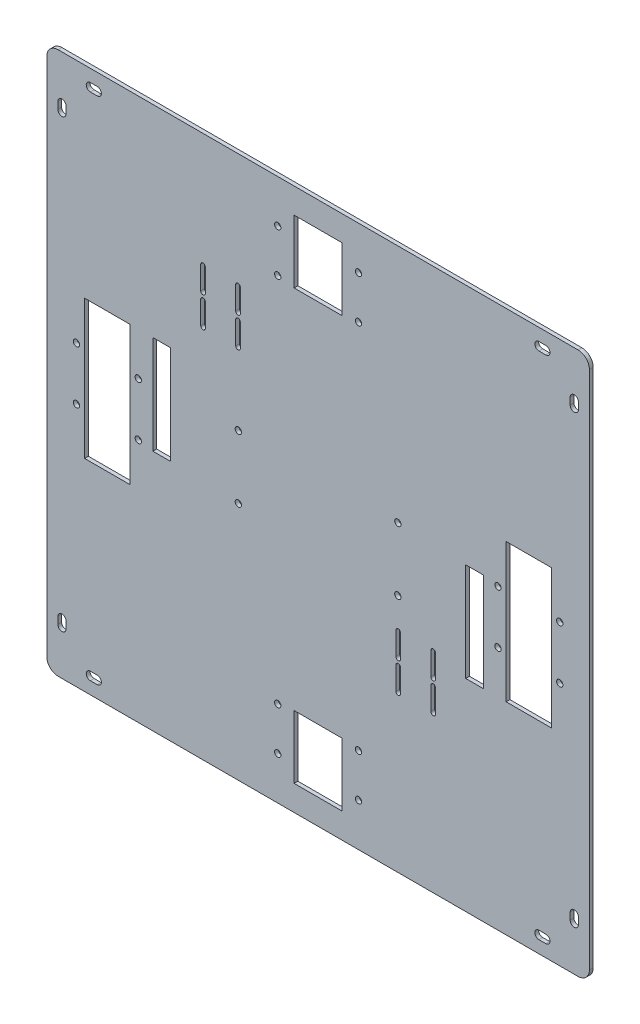
SolidWorks part; units mm, degrees
material "Alloy Steel (SS)"
ref_plane "Front Plane" through (0, 0, 0) normal (0, 0, 1) x (1, 0, 0)
ref_plane "Top Plane" through (0, 0, 0) normal (0, 1, 0) x (1, 0, 0)
ref_plane "Right Plane" through (0, 0, 0) normal (1, 0, 0) x (0, 0, -1)
sketch "Sketch1" plane through (0, 0, 0) normal (0, 0, 1) x (1, 0, 0)
  line L0 (0, 30.6518) -> (0, 116.7974) construction
  line L1 (215, 245.6518) -> (-215, 245.6518)
  line L2 (215, 245.6518) -> (215, -184.3482)
  line L3 (215, -184.3482) -> (-215, -184.3482)
  line L4 (-215, 245.6518) -> (-215, -184.3482)
  line L5 (215, 245.6518) -> (-215, -184.3482) construction
  line L6 (215, -184.3482) -> (-215, 245.6518) construction
  line L13 (0, 30.6518) -> (-105.2674, 30.6518) construction
  point P0 (0, 30.6518)
  dimension "D1" = 430
  dimension "D2" = 430
extrude "Boss-Extrude1" add sketch "Sketch1" along normal blind 3
sketch "Sketch6" plane through (0, 0, 3) normal (0, 0, 1) x (1, 0, 0)
  line L0 (-199.75, 204.6518) -> (-199.75, 210.1518) construction
  line L1 (-206.25, 210.1518) -> (-206.25, 204.6518) construction
  line L2 (-199.75, 204.6518) -> (-199.75, 210.1518)
  line L3 (-206.25, 210.1518) -> (-206.25, 204.6518)
  line L20 (-180.5, 229.4018) -> (-175, 229.4018) construction
  line L21 (-175, 235.9018) -> (-180.5, 235.9018) construction
  line L22 (-180.5, 229.4018) -> (-175, 229.4018)
  line L23 (-175, 235.9018) -> (-180.5, 235.9018)
  line L40 (0, 30.6518) -> (-215, 30.6518) construction
  line L41 (0, 30.6518) -> (-215, 30.6518) construction
  line L50 (-175, -174.5982) -> (-180.5, -174.5982)
  line L51 (-180.5, -168.0982) -> (-175, -168.0982)
  line L60 (-206.25, -148.8482) -> (-206.25, -143.3482)
  line L61 (-199.75, -143.3482) -> (-199.75, -148.8482)
  line L62 (0, 30.6518) -> (0, 245.6518) construction
  line L63 (0, 30.6518) -> (0, 245.6518) construction
  line L64 (199.75, -143.3482) -> (199.75, -148.8482)
  line L65 (206.25, -148.8482) -> (206.25, -143.3482)
  line L74 (180.5, -168.0982) -> (175, -168.0982)
  line L75 (175, -174.5982) -> (180.5, -174.5982)
  line L92 (175, 235.9018) -> (180.5, 235.9018)
  line L93 (180.5, 229.4018) -> (175, 229.4018)
  line L102 (206.25, 210.1518) -> (206.25, 204.6518)
  line L103 (199.75, 204.6518) -> (199.75, 210.1518)
  arc A0 (-206.25, 204.6518) -> (-199.75, 204.6518) centre (-203, 204.6518) ccw construction
  arc A1 (-199.75, 210.1518) -> (-206.25, 210.1518) centre (-203, 210.1518) ccw construction
  arc A2 (-206.25, 204.6518) -> (-199.75, 204.6518) centre (-203, 204.6518) ccw
  arc A3 (-199.75, 210.1518) -> (-206.25, 210.1518) centre (-203, 210.1518) ccw
  arc A4 (-175, 229.4018) -> (-175, 235.9018) centre (-175, 232.6518) ccw construction
  arc A5 (-180.5, 235.9018) -> (-180.5, 229.4018) centre (-180.5, 232.6518) ccw construction
  arc A6 (-175, 229.4018) -> (-175, 235.9018) centre (-175, 232.6518) ccw
  arc A7 (-180.5, 235.9018) -> (-180.5, 229.4018) centre (-180.5, 232.6518) ccw
  arc A8 (-180.5, -174.5982) -> (-180.5, -168.0982) centre (-180.5, -171.3482) cw
  arc A9 (-175, -168.0982) -> (-175, -174.5982) centre (-175, -171.3482) cw
  arc A10 (-199.75, -148.8482) -> (-206.25, -148.8482) centre (-203, -148.8482) cw
  arc A11 (-206.25, -143.3482) -> (-199.75, -143.3482) centre (-203, -143.3482) cw
  arc A12 (206.25, -143.3482) -> (199.75, -143.3482) centre (203, -143.3482) ccw
  arc A13 (199.75, -148.8482) -> (206.25, -148.8482) centre (203, -148.8482) ccw
  arc A14 (175, -168.0982) -> (175, -174.5982) centre (175, -171.3482) ccw
  arc A15 (180.5, -174.5982) -> (180.5, -168.0982) centre (180.5, -171.3482) ccw
  arc A16 (180.5, 235.9018) -> (180.5, 229.4018) centre (180.5, 232.6518) cw
  arc A17 (175, 229.4018) -> (175, 235.9018) centre (175, 232.6518) cw
  arc A18 (199.75, 210.1518) -> (206.25, 210.1518) centre (203, 210.1518) cw
  arc A19 (206.25, 204.6518) -> (199.75, 204.6518) centre (203, 204.6518) cw
extrude "Cut-Extrude5" cut sketch "Sketch6" against normal up to next
sketch "Sketch7" plane through (0, 0, 0) normal (0, 0, -1) x (-1, 0, 0)
  line L0 (0, 30.6518) -> (0, -184.3482) construction
  line L1 (185, -24.3482) -> (149, -24.3482)
  line L2 (185, -24.3482) -> (185, 85.6518)
  line L3 (185, 85.6518) -> (149, 85.6518)
  line L4 (149, -24.3482) -> (149, 85.6518)
  line L5 (185, -24.3482) -> (149, 85.6518) construction
  line L6 (185, 85.6518) -> (149, -24.3482) construction
  line L7 (215, -184.3482) -> (-215, -184.3482) construction
  line L8 (-185, 85.6518) -> (-149, -24.3482) construction
  line L9 (-185, -24.3482) -> (-149, 85.6518) construction
  line L10 (-149, -24.3482) -> (-149, 85.6518)
  line L11 (-185, 85.6518) -> (-149, 85.6518)
  line L12 (-185, -24.3482) -> (-185, 85.6518)
  line L13 (-185, -24.3482) -> (-149, -24.3482)
  line L14 (215, 245.6518) -> (215, -184.3482) construction
  point P0 (167, 30.6518)
  point P15 (-167, 30.6518)
  dimension "D1" = 36
  dimension "D2" = 110
  dimension "D3" = 30
extrude "Cut-Extrude6" cut sketch "Sketch7" against normal through all
sketch "Sketch9" plane through (0, 0, 0) normal (0, 0, -1) x (-1, 0, 0)
  line L0 (215, -184.3482) -> (-215, -184.3482) construction
  line L1 (-19, -164.3482) -> (19, -164.3482)
  line L2 (-19, -164.3482) -> (-19, -114.3482)
  line L3 (-19, -114.3482) -> (19, -114.3482)
  line L4 (19, -164.3482) -> (19, -114.3482)
  line L5 (0, 30.6518) -> (215, 30.6518) construction
  line L6 (0, 30.6518) -> (0, -148.8482) construction
  line L7 (19, 225.6518) -> (19, 175.6518)
  line L8 (-19, 175.6518) -> (19, 175.6518)
  line L9 (-19, 225.6518) -> (-19, 175.6518)
  line L10 (-19, 225.6518) -> (19, 225.6518)
  point P0 (0, -148.8482)
  point P17 (0, 210.1518)
  dimension "D1" = 20
  dimension "D2" = 38
  dimension "D3" = 50
extrude "Cut-Extrude7" cut sketch "Sketch9" against normal through all
sketch "Sketch10" plane through (0, 0, 0) normal (0, 0, -1) x (-1, 0, 0)
  line L0 (0, 30.6518) -> (215, 30.6518) construction
  circle A0 centre (32, -150.3482) radius 2.5 construction
  circle A1 centre (32, -150.3482) radius 2.5
  circle A2 centre (32, -116.3482) radius 2.5 construction
  circle A3 centre (32, -116.3482) radius 2.5
  circle A4 centre (-32, -116.3482) radius 2.5 construction
  circle A5 centre (-32, -116.3482) radius 2.5
  circle A6 centre (-32, -150.3482) radius 2.5 construction
  circle A7 centre (-32, -150.3482) radius 2.5
  circle A8 centre (-32, 211.6518) radius 2.5
  circle A9 centre (-32, 177.6518) radius 2.5
  circle A10 centre (32, 177.6518) radius 2.5
  circle A11 centre (32, 211.6518) radius 2.5
extrude "Cut-Extrude8" cut sketch "Sketch10" against normal through all
sketch "Sketch14" plane through (0, 0, 0) normal (0, 0, -1) x (-1, 0, 0)
  line L28 (215, 245.6518) -> (215, -184.3482) construction
  line L33 (117, 85.6518) -> (117, 7.6518)
  line L34 (131, 85.6518) -> (117, 85.6518)
  line L35 (131, 7.6518) -> (131, 85.6518)
  line L36 (-215, -184.3482) -> (-215, 245.6518) construction
  line L40 (-131, -24.3482) -> (-117, -24.3482)
  line L41 (-131, 53.6518) -> (-131, -24.3482)
  line L42 (-117, 53.6518) -> (-131, 53.6518)
  line L43 (-117, -24.3482) -> (-117, 53.6518)
  line L44 (131, 7.6518) -> (117, 7.6518)
  line L45 (185, 85.6518) -> (149, 85.6518) construction
  line L49 (-185, -24.3482) -> (-149, -24.3482) construction
  dimension "D2" = 84
  dimension "D3" = 14
  dimension "D1" = 84
  dimension "D4" = 14
  dimension "D5" = 78
  dimension "D6" = 78
extrude "Cut-Extrude11" cut sketch "Sketch14" against normal through all
sketch "Sketch15" plane through (0, 0, 0) normal (0, 0, -1) x (-1, 0, 0)
  line L0 (0, -184.3482) -> (0, 245.6518) construction
  line L18 (-61.63, -53.8932) -> (-61.63, -48.6932)
  line L19 (-65.28, -48.6932) -> (-65.28, -53.8932)
  line L20 (-61.63, -53.8932) -> (-61.63, -48.6932)
  line L21 (-65.28, -48.6932) -> (-65.28, -53.8932)
  line L22 (-61.63, -30.0032) -> (-61.63, -24.8032)
  line L23 (-65.28, -24.8032) -> (-65.28, -30.0032)
  line L24 (-61.63, -30.0032) -> (-61.63, -24.8032)
  line L25 (-65.28, -24.8032) -> (-65.28, -30.0032)
  line L26 (-89.38, -53.8932) -> (-89.38, -48.6932)
  line L27 (-93.03, -48.6932) -> (-93.03, -53.8932)
  line L28 (-89.38, -53.8932) -> (-89.38, -48.6932)
  line L29 (-93.03, -48.6932) -> (-93.03, -53.8932)
  line L30 (-89.38, -30.0032) -> (-89.38, -24.8032)
  line L31 (-93.03, -24.8032) -> (-93.03, -30.0032)
  line L32 (-89.38, -30.0032) -> (-89.38, -24.8032)
  line L33 (-93.03, -24.8032) -> (-93.03, -30.0032)
  line L50 (-63.455, -53.8932) -> (-63.455, -60.8932) construction
  line L51 (-61.63, -53.8932) -> (-61.63, -60.8932)
  line L52 (-65.28, -53.8932) -> (-65.28, -60.8932)
  line L53 (-91.205, -53.8932) -> (-91.205, -60.8932) construction
  line L54 (-89.38, -53.8932) -> (-89.38, -60.8932)
  line L55 (-93.03, -53.8932) -> (-93.03, -60.8932)
  line L56 (-63.455, -30.0032) -> (-63.455, -37.0032) construction
  line L57 (-61.63, -30.0032) -> (-61.63, -37.0032)
  line L58 (-65.28, -30.0032) -> (-65.28, -37.0032)
  line L59 (-91.205, -30.0032) -> (-91.205, -37.0032) construction
  line L60 (-89.38, -30.0032) -> (-89.38, -37.0032)
  line L61 (-93.03, -30.0032) -> (-93.03, -37.0032)
  line L62 (-63.455, -24.8032) -> (-63.455, -18.8032) construction
  line L63 (-65.28, -24.8032) -> (-65.28, -18.8032)
  line L64 (-61.63, -24.8032) -> (-61.63, -18.8032)
  line L65 (-63.455, -48.6932) -> (-63.455, -42.6932) construction
  line L66 (-65.28, -48.6932) -> (-65.28, -42.6932)
  line L67 (-61.63, -48.6932) -> (-61.63, -42.6932)
  line L68 (-91.205, -48.6932) -> (-91.205, -42.6932) construction
  line L69 (-93.03, -48.6932) -> (-93.03, -42.6932)
  line L70 (-89.38, -48.6932) -> (-89.38, -42.6932)
  line L71 (-91.205, -24.8032) -> (-91.205, -18.8032) construction
  line L72 (-93.03, -24.8032) -> (-93.03, -18.8032)
  line L73 (-89.38, -24.8032) -> (-89.38, -18.8032)
  line L103 (1.25, 31.6518) -> (-215, 31.6518) construction
  line L104 (-215, -184.3482) -> (-215, 245.6518) construction
  line L178 (91.205, 118.7587) -> (91.205, 112.7587) construction
  line L179 (93.03, 118.7587) -> (93.03, 112.7587)
  line L180 (89.38, 118.7587) -> (89.38, 112.7587)
  line L181 (91.205, 142.6487) -> (91.205, 136.6487) construction
  line L182 (93.03, 142.6487) -> (93.03, 136.6487)
  line L183 (89.38, 142.6487) -> (89.38, 136.6487)
  line L184 (63.455, 142.6487) -> (63.455, 136.6487) construction
  line L185 (65.28, 142.6487) -> (65.28, 136.6487)
  line L186 (61.63, 142.6487) -> (61.63, 136.6487)
  line L187 (63.455, 118.7587) -> (63.455, 112.7587) construction
  line L188 (65.28, 118.7587) -> (65.28, 112.7587)
  line L189 (61.63, 118.7587) -> (61.63, 112.7587)
  line L190 (91.205, 123.9587) -> (91.205, 130.9587) construction
  line L191 (89.38, 123.9587) -> (89.38, 130.9587)
  line L192 (93.03, 123.9587) -> (93.03, 130.9587)
  line L193 (63.455, 123.9587) -> (63.455, 130.9587) construction
  line L194 (61.63, 123.9587) -> (61.63, 130.9587)
  line L195 (65.28, 123.9587) -> (65.28, 130.9587)
  line L196 (91.205, 147.8487) -> (91.205, 154.8487) construction
  line L197 (89.38, 147.8487) -> (89.38, 154.8487)
  line L198 (93.03, 147.8487) -> (93.03, 154.8487)
  line L199 (63.455, 147.8487) -> (63.455, 154.8487) construction
  line L200 (61.63, 147.8487) -> (61.63, 154.8487)
  line L201 (65.28, 147.8487) -> (65.28, 154.8487)
  line L202 (61.63, 147.8487) -> (61.63, 142.6487)
  line L203 (65.28, 142.6487) -> (65.28, 147.8487)
  line L204 (61.63, 123.9587) -> (61.63, 118.7587)
  line L205 (65.28, 118.7587) -> (65.28, 123.9587)
  line L206 (89.38, 147.8487) -> (89.38, 142.6487)
  line L207 (93.03, 142.6487) -> (93.03, 147.8487)
  line L208 (89.38, 123.9587) -> (89.38, 118.7587)
  line L209 (93.03, 118.7587) -> (93.03, 123.9587)
  arc A18 (-65.28, -53.8932) -> (-61.63, -53.8932) centre (-63.455, -53.8932) ccw
  arc A19 (-61.63, -48.6932) -> (-65.28, -48.6932) centre (-63.455, -48.6932) ccw
  arc A20 (-65.28, -53.8932) -> (-61.63, -53.8932) centre (-63.455, -53.8932) ccw
  arc A21 (-61.63, -48.6932) -> (-65.28, -48.6932) centre (-63.455, -48.6932) ccw
  arc A22 (-61.63, -24.8032) -> (-65.28, -24.8032) centre (-63.455, -24.8032) ccw
  arc A23 (-65.28, -30.0032) -> (-61.63, -30.0032) centre (-63.455, -30.0032) ccw
  arc A24 (-61.63, -24.8032) -> (-65.28, -24.8032) centre (-63.455, -24.8032) ccw
  arc A25 (-65.28, -30.0032) -> (-61.63, -30.0032) centre (-63.455, -30.0032) ccw
  arc A26 (-93.03, -53.8932) -> (-89.38, -53.8932) centre (-91.205, -53.8932) ccw
  arc A27 (-89.38, -48.6932) -> (-93.03, -48.6932) centre (-91.205, -48.6932) ccw
  arc A28 (-93.03, -53.8932) -> (-89.38, -53.8932) centre (-91.205, -53.8932) ccw
  arc A29 (-89.38, -48.6932) -> (-93.03, -48.6932) centre (-91.205, -48.6932) ccw
  arc A30 (-89.38, -24.8032) -> (-93.03, -24.8032) centre (-91.205, -24.8032) ccw
  arc A31 (-93.03, -30.0032) -> (-89.38, -30.0032) centre (-91.205, -30.0032) ccw
  arc A32 (-89.38, -24.8032) -> (-93.03, -24.8032) centre (-91.205, -24.8032) ccw
  arc A33 (-93.03, -30.0032) -> (-89.38, -30.0032) centre (-91.205, -30.0032) ccw
  arc A44 (-61.63, -53.8932) -> (-65.28, -53.8932) centre (-63.455, -53.8932) ccw
  arc A45 (-65.28, -60.8932) -> (-61.63, -60.8932) centre (-63.455, -60.8932) ccw
  arc A46 (-89.38, -53.8932) -> (-93.03, -53.8932) centre (-91.205, -53.8932) ccw
  arc A47 (-93.03, -60.8932) -> (-89.38, -60.8932) centre (-91.205, -60.8932) ccw
  arc A48 (-61.63, -30.0032) -> (-65.28, -30.0032) centre (-63.455, -30.0032) ccw
  arc A49 (-65.28, -37.0032) -> (-61.63, -37.0032) centre (-63.455, -37.0032) ccw
  arc A50 (-89.38, -30.0032) -> (-93.03, -30.0032) centre (-91.205, -30.0032) ccw
  arc A51 (-93.03, -37.0032) -> (-89.38, -37.0032) centre (-91.205, -37.0032) ccw
  arc A52 (-65.28, -24.8032) -> (-61.63, -24.8032) centre (-63.455, -24.8032) ccw
  arc A53 (-61.63, -18.8032) -> (-65.28, -18.8032) centre (-63.455, -18.8032) ccw
  arc A54 (-65.28, -48.6932) -> (-61.63, -48.6932) centre (-63.455, -48.6932) ccw
  arc A55 (-61.63, -42.6932) -> (-65.28, -42.6932) centre (-63.455, -42.6932) ccw
  arc A56 (-93.03, -48.6932) -> (-89.38, -48.6932) centre (-91.205, -48.6932) ccw
  arc A57 (-89.38, -42.6932) -> (-93.03, -42.6932) centre (-91.205, -42.6932) ccw
  arc A58 (-93.03, -24.8032) -> (-89.38, -24.8032) centre (-91.205, -24.8032) ccw
  arc A59 (-89.38, -18.8032) -> (-93.03, -18.8032) centre (-91.205, -18.8032) ccw
  arc A140 (93.03, 118.7587) -> (89.38, 118.7587) centre (91.205, 118.7587) ccw
  arc A141 (89.38, 112.7587) -> (93.03, 112.7587) centre (91.205, 112.7587) ccw
  arc A142 (93.03, 142.6487) -> (89.38, 142.6487) centre (91.205, 142.6487) ccw
  arc A143 (89.38, 136.6487) -> (93.03, 136.6487) centre (91.205, 136.6487) ccw
  arc A144 (65.28, 142.6487) -> (61.63, 142.6487) centre (63.455, 142.6487) ccw
  arc A145 (61.63, 136.6487) -> (65.28, 136.6487) centre (63.455, 136.6487) ccw
  arc A146 (65.28, 118.7587) -> (61.63, 118.7587) centre (63.455, 118.7587) ccw
  arc A147 (61.63, 112.7587) -> (65.28, 112.7587) centre (63.455, 112.7587) ccw
  arc A148 (89.38, 123.9587) -> (93.03, 123.9587) centre (91.205, 123.9587) ccw
  arc A149 (93.03, 130.9587) -> (89.38, 130.9587) centre (91.205, 130.9587) ccw
  arc A150 (61.63, 123.9587) -> (65.28, 123.9587) centre (63.455, 123.9587) ccw
  arc A151 (65.28, 130.9587) -> (61.63, 130.9587) centre (63.455, 130.9587) ccw
  arc A152 (89.38, 147.8487) -> (93.03, 147.8487) centre (91.205, 147.8487) ccw
  arc A153 (93.03, 154.8487) -> (89.38, 154.8487) centre (91.205, 154.8487) ccw
  arc A154 (61.63, 147.8487) -> (65.28, 147.8487) centre (63.455, 147.8487) ccw
  arc A155 (65.28, 154.8487) -> (61.63, 154.8487) centre (63.455, 154.8487) ccw
  arc A156 (65.28, 147.8487) -> (61.63, 147.8487) centre (63.455, 147.8487) ccw
  arc A157 (61.63, 142.6487) -> (65.28, 142.6487) centre (63.455, 142.6487) ccw
  arc A158 (61.63, 118.7587) -> (65.28, 118.7587) centre (63.455, 118.7587) ccw
  arc A159 (65.28, 123.9587) -> (61.63, 123.9587) centre (63.455, 123.9587) ccw
  arc A160 (93.03, 147.8487) -> (89.38, 147.8487) centre (91.205, 147.8487) ccw
  arc A161 (89.38, 142.6487) -> (93.03, 142.6487) centre (91.205, 142.6487) ccw
  arc A162 (89.38, 118.7587) -> (93.03, 118.7587) centre (91.205, 118.7587) ccw
  arc A163 (93.03, 123.9587) -> (89.38, 123.9587) centre (91.205, 123.9587) ccw
  point P84 (-63.455, -57.3932)
  point P90 (-91.205, -57.3932)
  point P96 (-63.455, -33.5032)
  point P102 (-91.205, -33.5032)
  point P108 (-63.455, -21.8032)
  point P114 (-63.455, -45.6932)
  point P120 (-91.205, -45.6932)
  point P126 (-91.205, -21.8032)
  point P139 (91.205, 115.7587)
  point P146 (91.205, 139.6487)
  point P153 (63.455, 139.6487)
  point P164 (63.455, 115.7587)
  point P171 (91.205, 127.4587)
  point P178 (63.455, 127.4587)
  point P185 (91.205, 151.3487)
  point P192 (63.455, 151.3487)
  dimension "D11" = 7
  dimension "D12" = 6
  dimension "D5" = 0
  dimension "D6" = 0
  dimension "D7" = 0
  dimension "D8" = 0
extrude "Cut-Extrude12" cut sketch "Sketch15" against normal through all contours L52 A45 L51 A20 | A20 A44 | A54 L21 A44 L20 | A21 A54 | L67 A55 L66 A21 | L55 A47 L54 A28 | A28 A46 | A56 L29 A46 L28 | A29 A56 | L70 A57 L69 A29 | L58 A49 L57 A25 | A25 A48 | A52 L25 A48 L24 | A24 A52 | L64 A53 L63 A24 | L61 A51 L60 A33 | A33 A50 | A58 L33 A50 L32 | A32 A58 | L73 A59 L72 A32
fillet "Fillet1" radius 9 4 edges at (215, 245.6518, 1.5) (215, -184.3482, 1.5) (-215, 245.6518, 1.5) (-215, -184.3482, 1.5)
sketch "Sketch17" plane through (0, 0, 0) normal (0, 0, -1) x (-1, 0, 0)
  circle A0 centre (191.5, 51.6518) radius 2.5 construction
  circle A1 centre (191.5, 9.6518) radius 2.5 construction
  circle A2 centre (191.5, 51.6518) radius 2.5
  circle A3 centre (191.5, 9.6518) radius 2.5
  circle A4 centre (142.5, 51.6518) radius 2.5 construction
  circle A5 centre (142.5, 51.6518) radius 2.5
  circle A6 centre (142.5, 9.6518) radius 2.5 construction
  circle A7 centre (142.5, 9.6518) radius 2.5
  circle A8 centre (-191.5, 51.6518) radius 2.5 construction
  circle A9 centre (-191.5, 9.6518) radius 2.5 construction
  circle A10 centre (-191.5, 51.6518) radius 2.5
  circle A11 centre (-191.5, 9.6518) radius 2.5
  circle A12 centre (-142.5, 9.6518) radius 2.5 construction
  circle A13 centre (-142.5, 9.6518) radius 2.5
  circle A14 centre (-142.5, 51.6518) radius 2.5 construction
  circle A15 centre (-142.5, 51.6518) radius 2.5
  point P24 (0, 0)
extrude "Cut-Extrude13" cut sketch "Sketch17" against normal through all
sketch "Sketch18" plane through (0, 0, 0) normal (0, 0, -1) x (-1, 0, 0)
  circle A0 centre (63.2, 55.6518) radius 2.5 construction
  circle A1 centre (63.2, 5.6518) radius 2.5 construction
  circle A2 centre (63.2, 55.6518) radius 2.5
  circle A3 centre (63.2, 5.6518) radius 2.5
  circle A4 centre (-63.2, 55.6518) radius 2.5 construction
  circle A5 centre (-63.2, 5.6518) radius 2.5 construction
  circle A6 centre (-63.2, 55.6518) radius 2.5
  circle A7 centre (-63.2, 5.6518) radius 2.5
extrude "Cut-Extrude14" cut sketch "Sketch18" against normal through all
